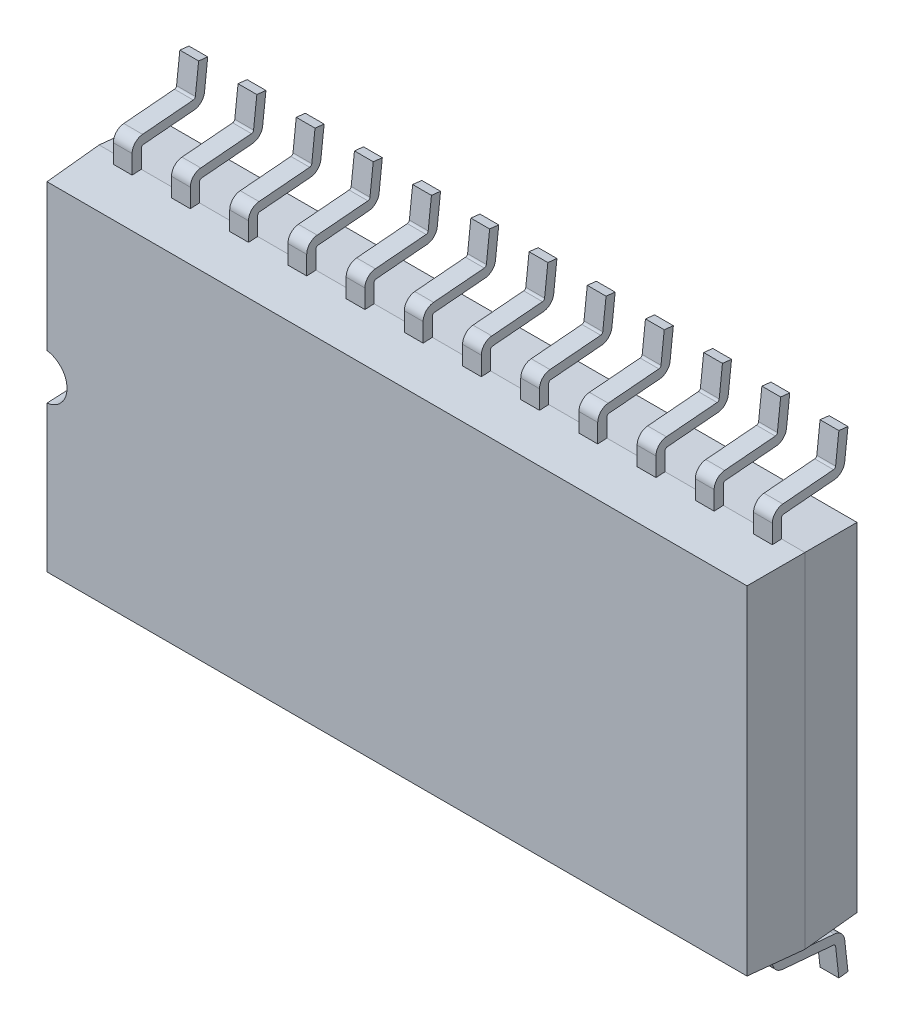
SolidWorks part; units mm, degrees
ref_plane "Front Plane" through (0, 0, 0) normal (0, 0, 1) x (1, 0, 0)
ref_plane "Top Plane" through (0, 0, 0) normal (0, 1, 0) x (1, 0, 0)
ref_plane "Right Plane" through (0, 0, 0) normal (1, 0, 0) x (0, 0, -1)
sketch "Sketch1" plane through (0, 0, 0) normal (0, 0, 1) x (1, 0, 0)
  line L1 (0, 0) -> (15.4, 0)
  line L2 (0, 0) -> (0, 7.5)
  line L3 (0, 7.5) -> (15.4, 7.5)
  line L4 (15.4, 0) -> (15.4, 7.5)
  dimension "D1" = 15.4
  dimension "D2" = 7.5
extrude "Boss-Extrude1" add sketch "Sketch1" along normal blind 1.2 draft 3
sketch "Sketch2" plane through (0, 0, 0) normal (0, 0, -1) x (-1, 0, 0)
  line L1 (-15.4, 0) -> (0, 0)
  line L2 (-15.4, 0) -> (-15.4, 7.5)
  line L3 (-15.4, 7.5) -> (0, 7.5)
  line L4 (0, 0) -> (0, 7.5)
extrude "Boss-Extrude2" add sketch "Sketch2" along normal blind 1.2 draft 3
ref_plane "Plane1" through (0.715, 0, 0) normal (1, 0, 0) x (0, 0, -1)
ref_plane "Plane2" through (0, 3.75, 0) normal (0, 1, 0) x (1, 0, 0)
sketch "Sketch3" plane through (0.715, 0, 0) normal (1, 0, 0) x (0, 0, -1)
  line L0 (0, 0.1748) -> (0, -0.4433)
  line L1 (0, 0) -> (0, 7.5) construction
  line L2 (0, -0.4433) -> (1.3559, -0.56)
  line L3 (1.3559, -0.56) -> (1.45, -1.4)
  dimension "D1" = 1.4
  dimension "D2" = 2.65
  dimension "D3" = 0.84
extrude "Extrude-Thin1" add sketch "Sketch3" along normal mid plane 0.41 thin
pattern_linear "LPattern1" count 12 spacing 1.27 along (1, 0, 0) of "Extrude-Thin1"
mirror "Mirror1" about plane through (0, 3.75, 0) normal (0, 1, 0) of "LPattern1", "Extrude-Thin1"
sketch "Sketch5" plane through (0, 0, 0) normal (0, 0, 1) x (1, 0, 0)
  line L1 (0, 7.5) -> (0, 0) construction
  line L2 (0, 4.25) -> (0, 3.25)
  arc A0 (0, 4.25) -> (0, 3.25) centre (0, 3.75) cw
  dimension "D1" = 0.5
extrude "Cut-Extrude4" cut sketch "Sketch5" along normal through all
